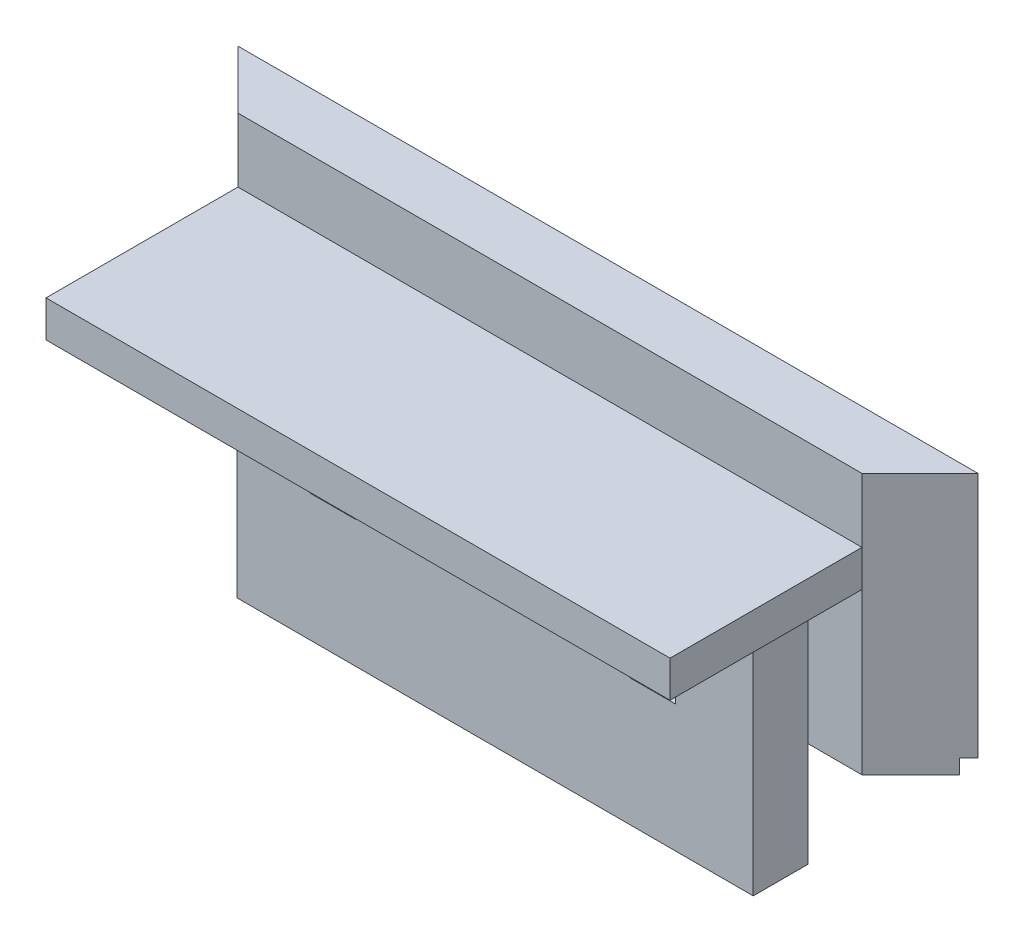
SolidWorks part; units mm, degrees
material "Beech"
ref_plane "Front Plane" through (0, 0, 0) normal (0, 0, 1) x (1, 0, 0)
ref_plane "Top Plane" through (0, 0, 0) normal (0, 1, 0) x (1, 0, 0)
ref_plane "Right Plane" through (0, 0, 0) normal (1, 0, 0) x (0, 0, -1)
other "Configuration Table"
sketch "Sketch1" plane through (0, 0, 0) normal (0, 1, 0) x (1, 0, 0)
  line L0 (-40.5003, 0) -> (40.5003, 0)
  line L1 (-40.5003, 0) -> (-34.1503, -6.35)
  line L2 (-34.1503, -6.35) -> (34.1503, -6.35)
  line L3 (34.1503, -6.35) -> (40.5003, 0)
  point P4 (0, 0)
  dimension "D1" = 81.0006
  dimension "D2" = 45
  dimension "D3" = 45
  dimension "D4" = 6.35
extrude "Boss-Extrude1" add sketch "Sketch1" along normal blind 28.575
sketch "Sketch2" plane through (0, 0, 0) normal (1, 0, 0) x (0, 0, -1)
  line L0 (0, 0) -> (0, 1.5875)
  line L1 (0, 28.575) -> (0, 0) construction
  line L2 (0, 1.5875) -> (-1.0008, 1.5875)
  line L3 (-1.0008, 1.5875) -> (-1.0008, 0)
  line L4 (-6.35, 0) -> (0, 0) construction
  line L5 (-1.0008, 0) -> (0, 0)
  dimension "D1" = 1.0008
  dimension "D2" = 1.5875
extrude "Cut-Extrude2" cut sketch "Sketch2" against normal through all both and the other way through all
sketch "Sketch3" plane through (0, 0, 6.35) normal (0, 0, 1) x (1, 0, 0)
  line L0 (-34.1503, 21.5646) -> (-34.1503, 17.5768)
  line L1 (-34.1503, 28.575) -> (-34.1503, 0) construction
  line L2 (-34.1503, 17.5768) -> (34.1503, 17.5768)
  line L3 (34.1503, 28.575) -> (34.1503, 0) construction
  line L4 (34.1503, 17.5768) -> (34.1503, 21.5646)
  line L5 (34.1503, 21.5646) -> (-34.1503, 21.5646)
  line L6 (-34.1503, 28.575) -> (34.1503, 28.575) construction
  dimension "D1" = 3.9878
  dimension "D2" = 7.0104
extrude "Boss-Extrude2" add sketch "Sketch3" along normal blind 21.0058
sketch "Sketch4" plane through (0, 0, 6.35) normal (0, 0, 1) x (1, 0, 0)
  line L0 (-34.1503, 17.5768) -> (34.1503, 17.5768) construction
  line L1 (-28.2448, -11.43) -> (28.2448, -11.43)
  line L2 (-28.2448, -11.43) -> (-28.2448, 17.5768)
  line L3 (-28.2448, 17.5768) -> (28.2448, 17.5768)
  line L4 (28.2448, -11.43) -> (28.2448, 17.5768)
  line L5 (-28.2448, -11.43) -> (28.2448, 17.5768) construction
  line L6 (-28.2448, 17.5768) -> (28.2448, -11.43) construction
  point P0 (0, 3.0734)
  dimension "D1" = 56.4896
  dimension "D2" = 29.0068
extrude "Boss-Extrude3" add sketch "Sketch4" along normal blind 5.9944
sketch "Sketch5" plane through (0, 0, 12.3444) normal (0, 0, 1) x (1, 0, 0)
  line L0 (-34.1503, 17.5768) -> (34.1503, 17.5768) construction
  line L1 (-20.2438, 17.5768) -> (-15.24, 17.5768)
  line L2 (-20.2438, 17.5768) -> (-20.2438, 2.4994)
  line L3 (-20.2438, 2.4994) -> (-15.24, 2.4994)
  line L4 (-15.24, 17.5768) -> (-15.24, 2.4994)
  line L5 (-28.2448, 17.5768) -> (-28.2448, -11.43) construction
  line L6 (14.7574, 17.5768) -> (19.7612, 17.5768)
  line L7 (14.7574, 17.5768) -> (14.7574, 2.4994)
  line L8 (14.7574, 2.4994) -> (19.7612, 2.4994)
  line L9 (19.7612, 17.5768) -> (19.7612, 2.4994)
  line L10 (-34.1503, 0) -> (-28.2448, 0) construction
  line L12 (28.2448, 0) -> (34.1503, 0) construction
  point P10 (-20.2438, 10.0381)
  dimension "D1" = 5.0038
  dimension "D2" = 8.001
  dimension "D3" = 29.9974
  dimension "D4" = 5.0038
  dimension "D5" = 2.4994
  dimension "D6" = 2.4994
extrude "Cut-Extrude3" cut sketch "Sketch5" against normal blind 5.9944
